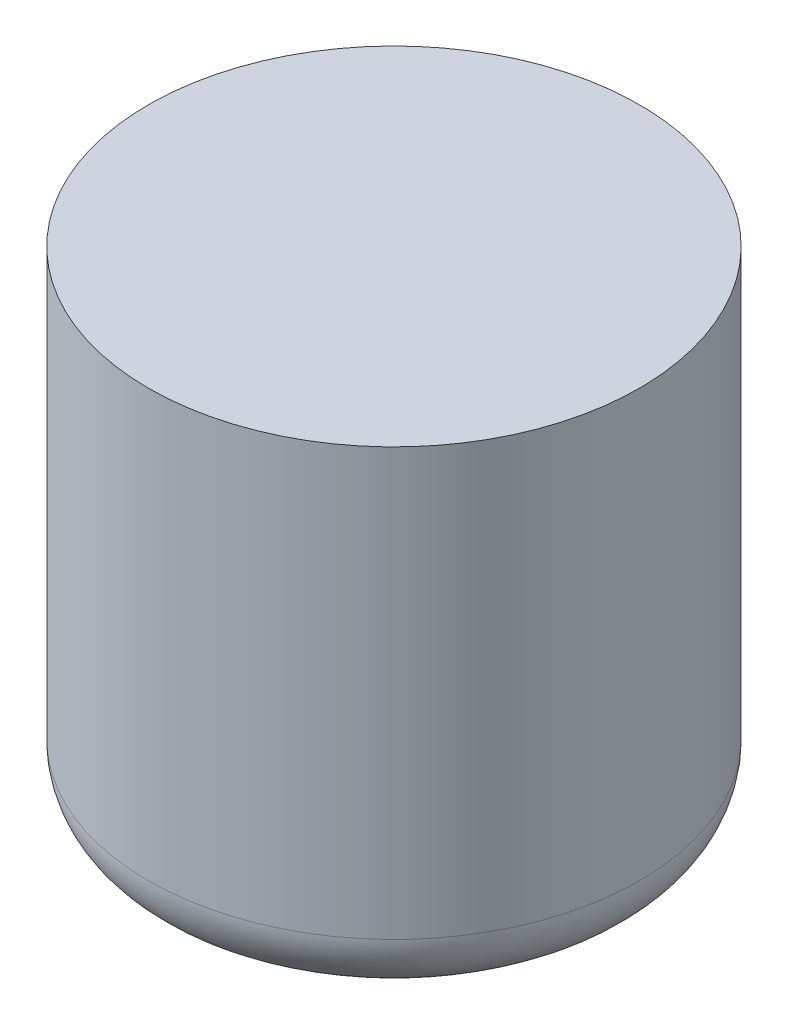
SolidWorks part; units mm, degrees
ref_plane "Front Plane" through (0, 0, 0) normal (0, 0, 1) x (1, 0, 0)
ref_plane "Top Plane" through (0, 0, 0) normal (0, 1, 0) x (1, 0, 0)
ref_plane "Right Plane" through (0, 0, 0) normal (1, 0, 0) x (0, 0, -1)
sketch "Sketch1" plane through (0, 0, 0) normal (0, 1, 0) x (1, 0, 0)
  circle A0 centre (0, 0) radius 19.05
  dimension "D1" = 38.1
extrude "Boss-Extrude1" add sketch "Sketch1" along normal blind 38.1
fillet "Fillet1" radius 5 1 edges at (0, 0, 19.05)
